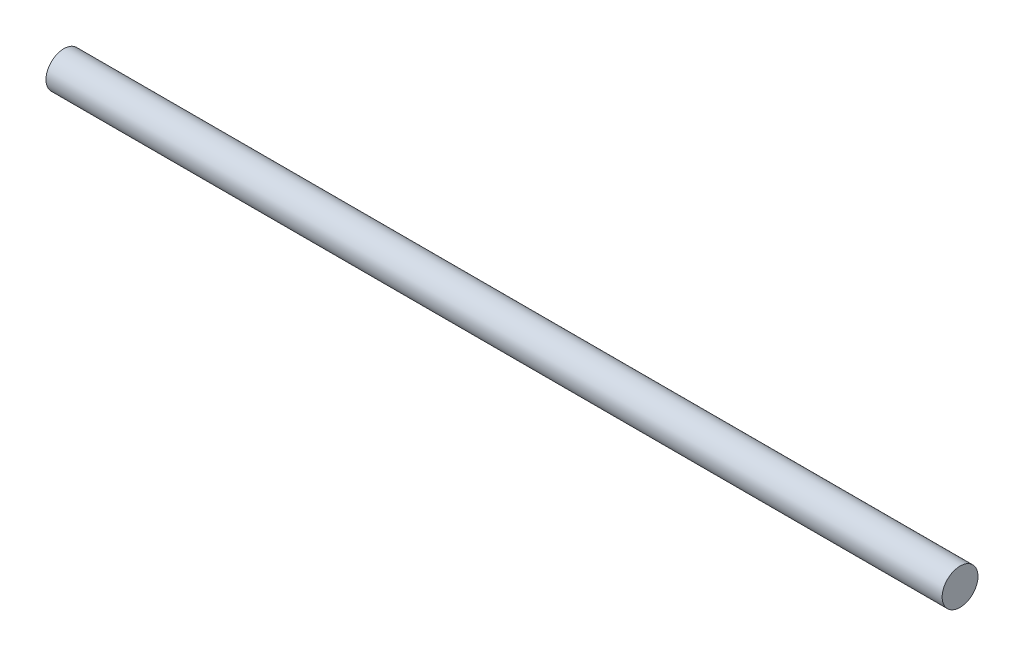
SolidWorks part; units mm, degrees
ref_plane "Front Plane" through (0, 0, 0) normal (0, 0, 1) x (1, 0, 0)
ref_plane "Top Plane" through (0, 0, 0) normal (0, 1, 0) x (1, 0, 0)
ref_plane "Right Plane" through (0, 0, 0) normal (1, 0, 0) x (0, 0, -1)
sketch "Sketch1" plane through (0, 0, 0) normal (1, 0, 0) x (0, 0, -1)
  circle A0 centre (0, 0) radius 17.5
extrude "Boss-Extrude2" add sketch "Sketch1" along normal mid plane 875 contours A0
